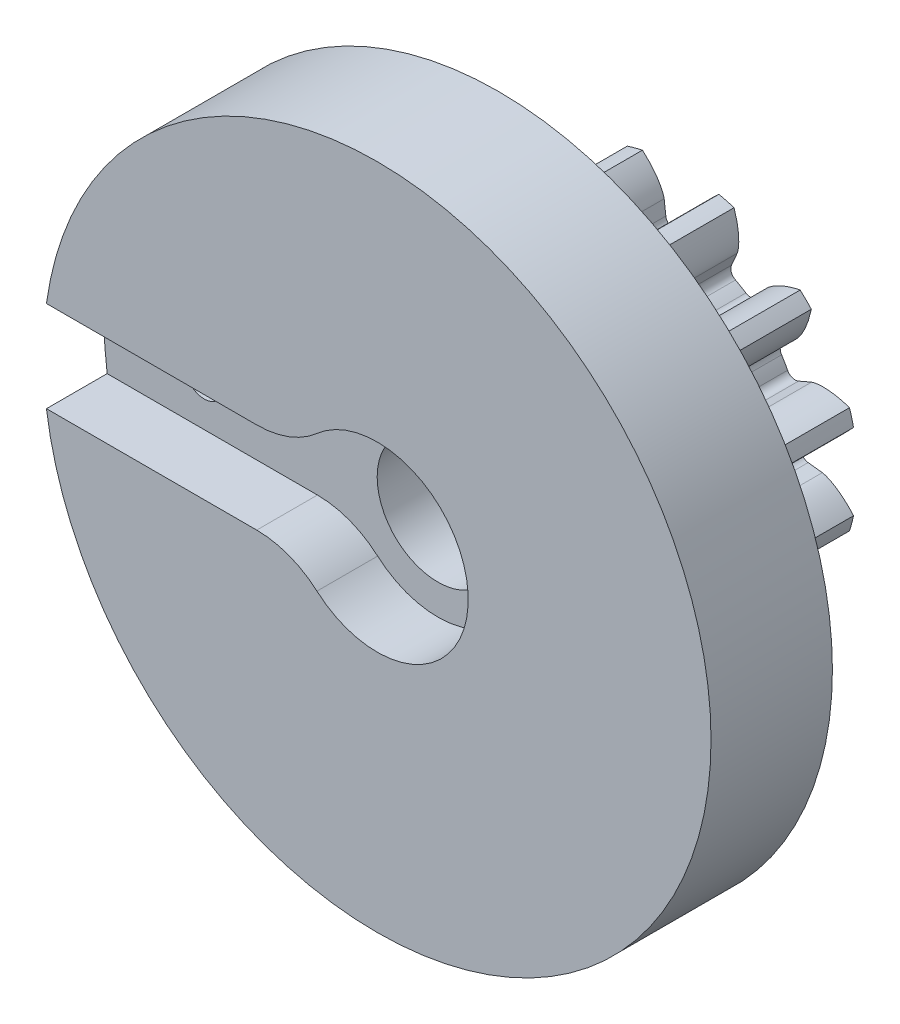
SolidWorks part; units mm, degrees
ref_plane "Front Plane" through (0, 0, 0) normal (0, 0, 1) x (1, 0, 0)
ref_plane "Top Plane" through (0, 0, 0) normal (0, 1, 0) x (1, 0, 0)
ref_plane "Right Plane" through (0, 0, 0) normal (1, 0, 0) x (0, 0, -1)
sketch "Sketch1" plane through (0, 0, 0) normal (0, 0, 1) x (1, 0, 0)
  line L0 (0, 0) -> (0, 6.35) construction
  line L1 (-2.0409, 7.0928) -> (2.0409, 5.6072) construction
  circle A0 centre (0, 0) radius 5.0271 construction
  circle A1 centre (0, 0) radius 7.4083 construction
  circle A2 centre (0, 0) radius 6.35 construction
  circle A3 centre (0, 0) radius 5.967 construction
  circle A4 centre (0, 0) radius 2.3813 construction
  circle A5 centre (0, 0) radius 4.826 construction
  point P8 (304.8, 0)
  point P13 (152.4, 0)
  dimension "OD | Outside Diameter" = 14.8167
  dimension "Root Diameter" = 10.0542
  dimension "Gear Pitch Diameter" = 12.7
  dimension "Base Diameter" = 11.9341
  dimension "For Shaft Diameter" = 4.7625
  dimension "Hub Diameter" = 9.652
  dimension "Pressure Angle" = 20
  dimension "Number of Teeth" = 304.8
  dimension "Gear Pitch | Diametral Pitch" = 609.6
sketch "Sketch2" plane through (0, 0, 0) normal (1, 0, 0) x (0, 0, -1)
  line L0 (-6.35, 0) -> (6.35, 0) construction
  line L1 (-6.35, 7.4083) -> (6.35, 7.4083) construction
  point P2 (0, 7.4083)
  point P4 (0, 0)
  point P6 (0, 7.4083)
  dimension "Overall Width" = 12.7
  dimension "Hub Width" = 6.35
  dimension "Face Width" = 6.35
sketch "Sketch3" plane through (0, 0, 0) normal (0, 0, 1) x (1, 0, 0)
  circle A0 centre (0, 0) radius 7.4083
  circle A1 centre (0, 0) radius 7.4083 construction
extrude "Boss-Extrude1" add sketch "Sketch3" against normal blind 7.62
sketch "Sketch4" plane through (0, 0, 0) normal (0, 0, 1) x (1, 0, 0)
  line L0 (0, 0) -> (4.9933, 0.5818) construction
  line L2 (0, 0) -> (4.9933, -0.5818) construction
  line L4 (4.9933, 0.5818) -> (5.927, 0.6906)
  line L5 (5.927, -0.6906) -> (4.9933, -0.5818)
  arc A0 (4.9933, 0.5818) -> (4.9933, -0.5818) centre (0, 0) cw
  arc A3 (7.2339, 1.5983) -> (7.2339, -1.5983) centre (0, 0) cw
  circle A4 centre (0, 0) radius 7.4083 construction
  spline S0 degree 4 poles (5.927, 0.6906) (5.9293, 0.6909) (5.9359, 0.6919) (5.9484, 0.6942) (5.9686, 0.6987) (5.9942, 0.7052) (6.0271, 0.7148) (6.0655, 0.7275) (6.1073, 0.7428) (6.1523, 0.761) (6.1969, 0.7804) (6.2409, 0.8011) (6.2844, 0.8228) (6.3367, 0.8503) (6.3986, 0.8852) (6.47, 0.9285) (6.5497, 0.9807) (6.6294, 1.0371) (6.7066, 1.0952) (6.7832, 1.1568) (6.8562, 1.2185) (6.9304, 1.2856) (6.9981, 1.3489) (7.0721, 1.4232) (7.1312, 1.484) (7.2071, 1.5675) (7.2513, 1.6179) (7.3023, 1.6779) (7.3245, 1.7051) (7.3382, 1.7219) knots 0 0 0 0 0 0.005377 0.015084 0.028532 0.04661 0.064855 0.092111 0.119476 0.146842 0.174209 0.201575 0.228941 0.256307 0.307035 0.361767 0.4165 0.471232 0.525964 0.580697 0.635429 0.690161 0.744894 0.799626 0.854358 0.909091 0.954545 1 1 1 1 1 construction
  spline S1 degree 4 poles (5.927, 0.6906) (5.9293, 0.6909) (5.9359, 0.6919) (5.9484, 0.6942) (5.9686, 0.6987) (5.9942, 0.7052) (6.0271, 0.7148) (6.0655, 0.7275) (6.1073, 0.7428) (6.1523, 0.761) (6.1969, 0.7804) (6.2409, 0.8011) (6.2844, 0.8228) (6.3367, 0.8503) (6.3986, 0.8852) (6.47, 0.9285) (6.5497, 0.9807) (6.6294, 1.0371) (6.7066, 1.0952) (6.7832, 1.1568) (6.8562, 1.2185) (6.9304, 1.2856) (6.9981, 1.3489) (7.0721, 1.4232) (7.1312, 1.484) (7.1906, 1.5494) (7.2193, 1.5816) (7.2339, 1.5983) knots 0 0 0 0 0 0.005377 0.015084 0.028532 0.04661 0.064855 0.092111 0.119476 0.146842 0.174209 0.201575 0.228941 0.256307 0.307035 0.361767 0.4165 0.471232 0.525964 0.580697 0.635429 0.690161 0.744894 0.799626 0.854358 0.909091 0.909091 0.909091 0.909091 0.909091
  spline S2 degree 4 poles (5.927, -0.6906) (5.9293, -0.6909) (5.9359, -0.6919) (5.9484, -0.6942) (5.9686, -0.6987) (5.9942, -0.7052) (6.0271, -0.7148) (6.0655, -0.7275) (6.1073, -0.7428) (6.1523, -0.761) (6.1969, -0.7804) (6.2409, -0.8011) (6.2844, -0.8228) (6.3367, -0.8503) (6.3986, -0.8852) (6.47, -0.9285) (6.5497, -0.9807) (6.6294, -1.0371) (6.7066, -1.0952) (6.7832, -1.1568) (6.8562, -1.2185) (6.9304, -1.2856) (6.9981, -1.3489) (7.0721, -1.4232) (7.1312, -1.484) (7.2071, -1.5675) (7.2513, -1.6179) (7.3023, -1.6779) (7.3245, -1.7051) (7.3382, -1.7219) knots 0 0 0 0 0 0.005377 0.015084 0.028532 0.04661 0.064855 0.092111 0.119476 0.146842 0.174209 0.201575 0.228941 0.256307 0.307035 0.361767 0.4165 0.471232 0.525964 0.580697 0.635429 0.690161 0.744894 0.799626 0.854358 0.909091 0.954545 1 1 1 1 1 construction
  spline S3 degree 4 poles (5.927, -0.6906) (5.9293, -0.6909) (5.9359, -0.6919) (5.9484, -0.6942) (5.9686, -0.6987) (5.9942, -0.7052) (6.0271, -0.7148) (6.0655, -0.7275) (6.1073, -0.7428) (6.1523, -0.761) (6.1969, -0.7804) (6.2409, -0.8011) (6.2844, -0.8228) (6.3367, -0.8503) (6.3986, -0.8852) (6.47, -0.9285) (6.5497, -0.9807) (6.6294, -1.0371) (6.7066, -1.0952) (6.7832, -1.1568) (6.8562, -1.2185) (6.9304, -1.2856) (6.9981, -1.3489) (7.0721, -1.4232) (7.1312, -1.484) (7.1906, -1.5494) (7.2193, -1.5816) (7.2339, -1.5983) knots 0 0 0 0 0 0.005377 0.015084 0.028532 0.04661 0.064855 0.092111 0.119476 0.146842 0.174209 0.201575 0.228941 0.256307 0.307035 0.361767 0.4165 0.471232 0.525964 0.580697 0.635429 0.690161 0.744894 0.799626 0.854358 0.909091 0.909091 0.909091 0.909091 0.909091
  dimension "D1" = 10.0542
extrude "Cut-Extrude1" cut sketch "Sketch4" against normal through all both and the other way through all
fillet "Fillet1" radius 0.3551 2 edges at (4.9933, -0.5818, -3.81) (4.9933, 0.5818, -3.81)
pattern_circular "CirPattern1" count 12 over 360 about axis through (0, 0, 6.35) along (0, 0, -1) of "Cut-Extrude1", "Fillet1"
scale "Scale1" bodies to scale 106 scale about origin uniform scaling yes scale factor 2
sketch "Sketch10" plane through (0, 0, 0) normal (0, 0, 1) x (1, 0, 0)
  circle A0 centre (0, 0) radius 27.94
extrude "Boss-Extrude4" add sketch "Sketch10" along normal blind 10.16
sketch "Sketch11" plane through (0, 0, -15.24) normal (0, 0, -1) x (-1, 0, 0)
  circle A0 centre (0, 0) radius 5.08
extrude "Cut-Extrude5" cut sketch "Sketch11" against normal through all
sketch "Sketch12" plane through (0, 0, 10.16) normal (0, 0, 1) x (1, 0, 0)
  line L1 (-10.0803, -3.81) -> (-28.4386, -3.81)
  line L3 (-10.0803, 3.81) -> (-28.4386, 3.81)
  line L4 (-28.4386, -3.81) -> (-28.4386, 3.81)
  arc A0 (-5.0402, -5.715) -> (-5.0402, 5.715) centre (0, 0) ccw
  arc A1 (-10.0803, -3.81) -> (-5.0402, -5.715) centre (-10.0803, -11.43) cw
  arc A2 (-10.0803, 3.81) -> (-5.0402, 5.715) centre (-10.0803, 11.43) ccw
  point P10 (-28.4386, 0)
  dimension "D1" = 7.62
  dimension "D2" = 7.62
  dimension "D3" = 7.62
extrude "Cut-Extrude6" cut sketch "Sketch12" against normal blind 5.08
sketch "Sketch13" plane through (0, 0, 5.08) normal (0, 0, 1) x (1, 0, 0)
  line L0 (0, 0) -> (0, 18.2969) construction
  circle A0 centre (-19.558, 0) radius 1.5875
  dimension "D1" = 3.175
  dimension "D2" = 19.558
extrude "Cut-Extrude12" cut sketch "Sketch13" against normal through all
sketch "Sketch16" plane through (0, 0, 0) normal (0, 0, -1) x (-1, 0, 0)
  circle A0 centre (19.558, 0) radius 2.7496
  dimension "D1" = 5.4991
extrude "Cut-Extrude13" cut sketch "Sketch16" against normal blind 3.81
sketch "Sketch17" plane through (0, 0, -15.24) normal (0, 0, -1) x (-1, 0, 0)
  circle A0 centre (0, 0) radius 12.7
equation "\"Root Diameter@Sketch1\"=\"Root Diameter\""
equation "\"OD | Outside Diameter@Sketch1\"=\"Outside Diameter\""
equation "\"D1@CirPattern1\"=\"Number of Teeth\""
equation "\"Diametral Pitch\"= 24"
equation "\"Number of Teeth\"= 12"
equation "\"Pressure Angle\"=20"
equation "\"Pitch Diameter\"= \"Number of Teeth\" / \"Diametral Pitch\""
equation "\"Base Diameter\"= \"Pitch Diameter\" * cos ( \"Pressure Angle\" )"
equation "\"Outside Diameter\"= ( \"Number of Teeth\" + 2 ) / \"Diametral Pitch\""
equation "\"Dedendum\"= 1.25 / \"Diametral Pitch\""
equation "\"Root Diameter\"= \"Pitch Diameter\" - ( 2 * \"Dedendum\" )"
equation "\"Pitch Angle\"= 360deg / \"Number of Teeth\""
equation "\"Alpha\"= sqr ( \"Pitch Diameter\" ^ 2 - \"Base Diameter\" ^ 2 ) / \"Base Diameter\" * 180 / PI - \"Pressure Angle\""
equation "\"Beta\"= ( \"Pitch Angle\" / 4 - \"Alpha\" )"
equation "\"Phi\"= sqr ( ( \"Outside Diameter\" / 2 ) ^ 2 - ( \"Base Diameter\" / 2 ) ^ 2 ) / ( \"Base Diameter\" / 2 )"
equation "\"Addendum\"= 1 / \"Diametral Pitch\""
equation "\"WorkingDepth\"= 2 / \"Diametral Pitch\""
equation "\"WholeDepth\"= 2.25 / \"Diametral Pitch\""
equation "\"Clearance\"= 0.25 / \"Diametral Pitch\""
equation "\"ToothThickness\"= ( pi * 2 ) / \"Diametral Pitch\""
equation "\"CircularPitch\"= pi / \"Diametral Pitch\""
equation "\"Number of Teeth@Sketch1\"=\"Number of Teeth\""
equation "\"Gear Pitch | Diametral Pitch@Sketch1\"=\"Diametral Pitch\""
equation "\"Pressure Angle@Sketch1\"=\"Pressure Angle\""
equation "\"Gear Pitch Diameter@Sketch1\"=\"Pitch Diameter\""
equation "\"Base Diameter@Sketch1\"=\"Base Diameter\""
equation "\"Fillet\"= \"Clearance\" * cos ( \"Pressure Angle\" ) * tan ( ( 90 + \"Pressure Angle\" ) / 2 )"
equation "\"D1@Fillet1\"=\"Fillet\""
equation "\"D1@Sketch4\"=if( \"Base Diameter\">\"Root Diameter\",\"Root Diameter\",\"Base Diameter\"-.00001)"
equation "\"D1@Fillet2\"=\"Fillet\""
